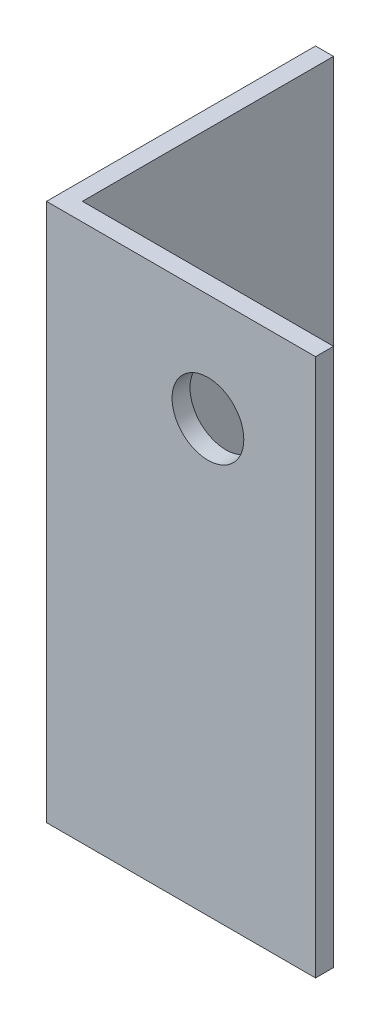
SolidWorks part; units mm, degrees
ref_plane "Спереди" through (0, 0, 0) normal (0, 0, 1) x (1, 0, 0)
ref_plane "Сверху" through (0, 0, 0) normal (0, 1, 0) x (1, 0, 0)
ref_plane "Справа" through (0, 0, 0) normal (1, 0, 0) x (0, 0, -1)
sketch "Эскиз1" plane through (0, 0, 0) normal (0, 1, 0) x (1, 0, 0)
  line L0 (0, 75) -> (0, 0)
  line L1 (0, 0) -> (75, 0)
extrude "Вытянуть-Тонкостенный1" add sketch "Эскиз1" along normal blind 150 thin thin type one direction reverse wall 5
sketch "Эскиз2" plane through (0, 0, 0) normal (0, 0, 1) x (1, 0, 0)
  line L0 (75, 150) -> (75, 0) construction
  line L1 (0, 150) -> (75, 150) construction
  circle A0 centre (45, 120) radius 10
  point P2 (0, 0)
  dimension "D1" = 30
  dimension "D2" = 30
extrude "Вырез-Вытянуть1" cut sketch "Эскиз2" against normal through all
